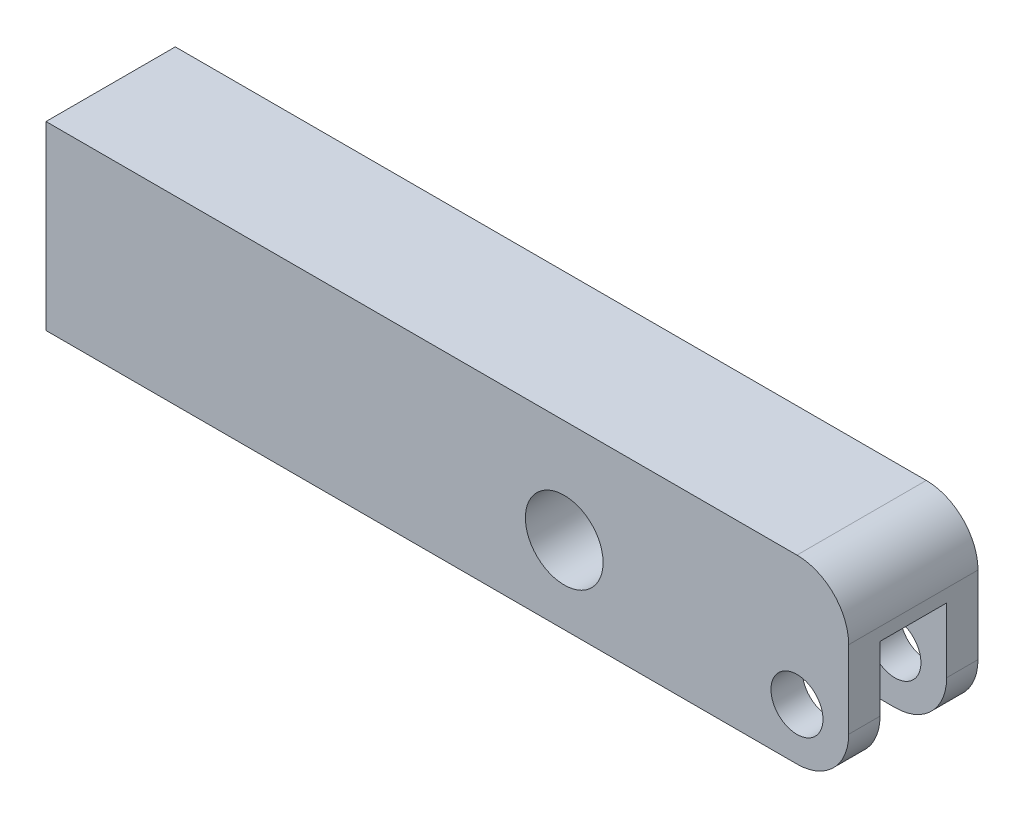
SolidWorks part; units mm, degrees
material "Alloy Steel"
ref_plane "Front Plane" through (0, 0, 0) normal (0, 0, 1) x (1, 0, 0)
ref_plane "Top Plane" through (0, 0, 0) normal (0, 1, 0) x (1, 0, 0)
ref_plane "Right Plane" through (0, 0, 0) normal (1, 0, 0) x (0, 0, -1)
sketch "Sketch11" plane through (0, 0, 0) normal (0, 0, 1) x (1, 0, 0)
  line L1 (-92.202, 15.875) -> (6.35, 15.875)
  line L2 (-92.202, 15.875) -> (-92.202, -6.35)
  line L3 (-92.202, -6.35) -> (6.35, -6.35)
  line L4 (6.35, 15.875) -> (6.35, -6.35)
  circle A0 centre (0, 0) radius 3.194
  circle A1 centre (-28.575, 3.175) radius 4.7689
  dimension "D1" = 6.3881
  dimension "D6" = 9.5377
  dimension "D2" = 6.35
  dimension "D3" = 92.202
  dimension "D4" = 22.225
  dimension "D5" = 28.575
  dimension "D7" = 6.35
  dimension "D8" = 3.175
extrude "Extrude3" add sketch "Sketch11" along normal mid plane 15.875
sketch "Sketch12" plane through (0, -6.35, 0) normal (0, -1, 0) x (1, 0, 0)
  line L0 (0, 0) -> (-16.2248, 0) construction
  line L1 (-7.9248, 4.0894) -> (6.35, 4.0894)
  line L2 (6.35, 7.9375) -> (6.35, -7.9375) construction
  line L3 (6.35, 4.0894) -> (6.35, -4.0894)
  line L4 (-92.202, 7.9375) -> (6.35, 7.9375) construction
  line L5 (-7.9248, -4.0894) -> (6.35, -4.0894)
  arc A0 (-7.9248, 4.0894) -> (-7.9248, -4.0894) centre (-7.9248, 0) ccw
  dimension "D3" = 18.3642
  dimension "D1" = 8.1788
  dimension "D2" = 3.8481
extrude "Cut-Extrude1" cut sketch "Sketch12" against normal blind 14.3002
fillet "Fillet1" radius 6.35 3 edges at (6.35, 15.875, 0) (6.35, -6.35, -6.0134) (6.35, -6.35, 6.0134)
